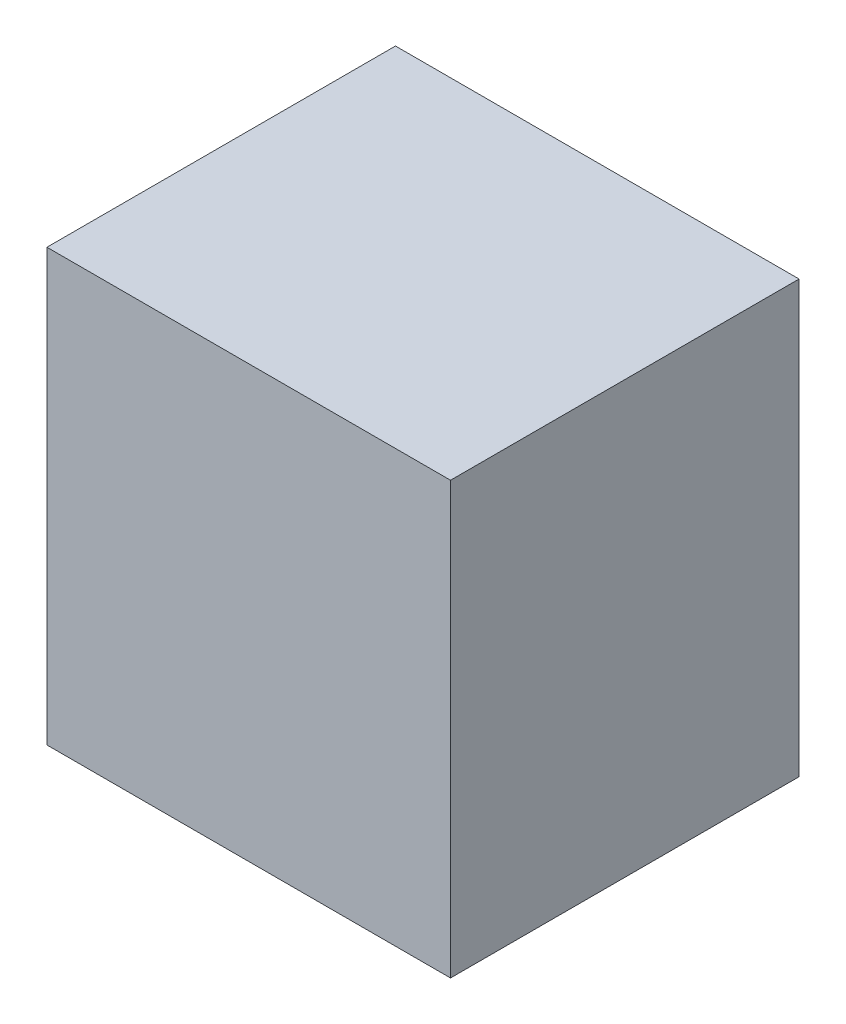
SolidWorks part; units mm, degrees
ref_plane "Front Plane" through (0, 0, 0) normal (0, 0, 1) x (1, 0, 0)
ref_plane "Top Plane" through (0, 0, 0) normal (0, 1, 0) x (1, 0, 0)
ref_plane "Right Plane" through (0, 0, 0) normal (1, 0, 0) x (0, 0, -1)
sketch "Sketch2" plane through (0, 0, 0) normal (0, 1, 0) x (1, 0, 0)
  line L1 (0, 0) -> (88, 0)
  line L2 (0, 0) -> (0, 76)
  line L3 (0, 76) -> (88, 76)
  line L4 (88, 0) -> (88, 76)
  dimension "D1" = 76
  dimension "D2" = 88
extrude "Boss-Extrude1" add sketch "Sketch2" along normal blind 94
